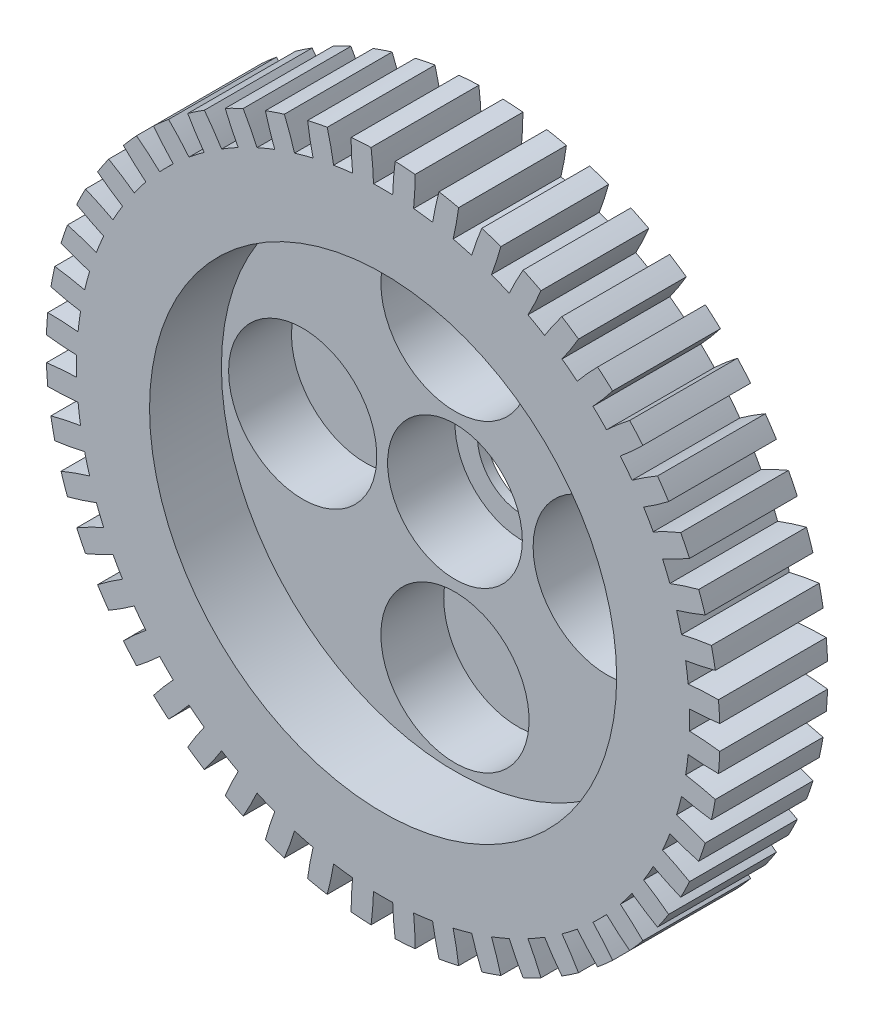
SolidWorks part; units mm, degrees
ref_plane "Piano frontale" through (0, 0, 0) normal (0, 0, 1) x (1, 0, 0)
ref_plane "Piano superiore" through (0, 0, 0) normal (0, 1, 0) x (1, 0, 0)
ref_plane "Piano destro" through (0, 0, 0) normal (1, 0, 0) x (0, 0, -1)
sketch "Schizzo1" plane through (0, 0, 0) normal (0, 0, 1) x (1, 0, 0)
  circle A0 centre (0, 0) radius 37.5
  dimension "D1" = 75
extrude "Estrusione-Estrusione2" add sketch "Schizzo1" along normal blind 12
sketch "Schizzo8" plane through (0, 0, 0) normal (0, 0, -1) x (-1, 0, 0)
  circle A0 centre (0, 0) radius 30
  dimension "D1" = 60
extrude "Taglio-Estrusione4" cut sketch "Schizzo8" against normal blind 2
sketch "Schizzo2" plane through (0, 0, 12) normal (0, 0, 1) x (1, 0, 0)
  circle A0 centre (0, 0) radius 26
  dimension "D1" = 52
extrude "Taglio-Estrusione1" cut sketch "Schizzo2" against normal blind 8
sketch "Schizzo4" plane through (0, 0, 0) normal (0, 0, -1) x (-1, 0, 0)
  circle A0 centre (0, 0) radius 8.5
  circle A1 centre (0, 0) radius 5
  dimension "D1" = 17
  dimension "D2" = 10
extrude "Estrusione-Estrusione3" add sketch "Schizzo4" along normal blind 6.5 from surface at -2 starting at face at (-30, 0, 2)
sketch "Schizzo3" plane through (0, 0, 4) normal (0, 0, 1) x (1, 0, 0)
  circle A0 centre (0, 0) radius 7.5
  dimension "D1" = 15
extrude "Taglio-Estrusione2" cut sketch "Schizzo3" against normal blind 7.5
sketch "Schizzo5" plane through (0, 0, 0) normal (0, 0, -1) x (-1, 0, 0)
  line L1 (-26.2, 0) -> (26.2, 0) construction
  circle A2 centre (0, 16.95) radius 9.25
  circle A7 centre (16.95, 0) radius 9.25
  circle A9 centre (0, -16.95) radius 9.25
  circle A10 centre (-16.95, 0) radius 9.25
  point P18 (0, 0)
  dimension "D1" = 18.5
  dimension "D2" = 4
  dimension "D4" = 52.4
extrude "Estrusione-Estrusione6" add sketch "Schizzo5" along normal blind 6.5 from surface at -2 starting at face at (-8.5, 0, 2)
sketch "Schizzo6" plane through (0, 0, -4.5) normal (0, 0, -1) x (-1, 0, 0)
  line L0 (0, 0) -> (0, 16.95) construction
  circle A0 centre (0, 16.95) radius 8.25
  circle A4 centre (16.95, 0) radius 8.25
  circle A5 centre (0, -16.95) radius 8.25
  circle A6 centre (-16.95, 0) radius 8.25
  dimension "D1" = 16.5
  dimension "D3" = 16.95
  dimension "D2" = 4
extrude "Taglio-Estrusione3" cut sketch "Schizzo6" along normal blind 7 from offset 8.5 offset against normal yes
sketch "Schizzo10" plane through (0, 0, 12) normal (0, 0, 1) x (1, 0, 0)
  line L0 (0, 0) -> (37.5, 0) construction
  line L1 (0, 0) -> (34.1083, -1.0677) construction
  line L2 (0, 0) -> (34.1083, 1.0677) construction
  arc A0 (35.9807, -1.178) -> (35.9807, 1.178) centre (0, 0) ccw construction
  arc A2 (34.1083, -1.0677) -> (34.1083, 1.0677) centre (0, 0) ccw
  arc A3 (37.4761, -1.3399) -> (37.4761, 1.3399) centre (0, 0) ccw
  circle A4 centre (0, 0) radius 37.5 construction
  spline S0 degree 4 poles (24.9625, -68.4576) (25.0835, -68.4874) (25.3257, -68.5458) (25.8112, -68.6578) (26.5426, -68.8117) (27.2776, -68.9478) (28.0156, -69.066) (28.7518, -69.1692) (29.3644, -69.243) (29.9762, -69.3049) (30.5873, -69.3549) (31.0764, -69.3879) (31.5666, -69.4138) (32.0556, -69.4328) (32.5818, -69.4453) (33.1334, -69.4505) (33.7369, -69.4447) (34.2613, -69.4315) (34.7521, -69.4104) (35.213, -69.3851) (35.466, -69.3686) (35.981, -69.3305) (36.3975, -69.2924) (36.846, -69.2464) (37.2899, -69.1949) (37.7329, -69.1376) (38.1752, -69.0744) (38.6168, -69.0055) (39.0573, -68.9309) (39.8265, -68.7901) (42.0132, -68.3305) (44.9107, -67.4661) (48.0036, -66.1458) (51.3092, -64.2674) (53.8863, -62.4893) (56.3007, -60.4921) (58.8065, -57.9338) (61.0314, -55.1278) (62.7111, -52.4827) (63.9471, -50.1005) (65.0135, -47.6395) (65.9064, -45.1086) (66.8884, -41.2947) (67.5021, -36.038) (67.1632, -29.8392) (65.5656, -23.8379) (63.2992, -18.9535) (60.6273, -14.8177) (58.0435, -11.7211) (55.4291, -9.2684) (52.935, -7.3757) (51.0649, -6.1515) (49.5199, -5.2516) (48.1287, -4.5357) (46.911, -3.9746) (45.8806, -3.5426) (45.0478, -3.2186) (44.2065, -2.9165) (43.3582, -2.6364) (42.5055, -2.3796) (41.6523, -2.1461) (40.7935, -1.9355) (39.9396, -1.7479) (39.0706, -1.582) (38.2159, -1.4388) (37.3264, -1.3169) (36.489, -1.219) (35.6426, -1.1482) (35.039, -1.1055) (34.3288, -1.0747) (34.0395, -1.0648) (33.5646, -1.0543) (33.0275, -1.0483) (32.492, -1.0532) (31.8232, -1.0694) (31.1807, -1.0987) (30.5266, -1.14) (29.8794, -1.1939) (29.2303, -1.2599) (28.5841, -1.3383) (27.9388, -1.4289) (27.2957, -1.5318) (26.4941, -1.6756) (25.6965, -1.8397) (24.9033, -2.0238) (24.2727, -2.1872) (23.9584, -2.2728) (23.8016, -2.3166) knots 0 0 0 0 0 0.003984 0.007969 0.015937 0.023906 0.02789 0.031875 0.039718 0.04364 0.047561 0.051483 0.055404 0.059326 0.063248 0.068241 0.073234 0.078227 0.080724 0.08322 0.086793 0.090366 0.09394 0.097513 0.101086 0.104659 0.108232 0.111805 0.115378 0.118951 0.133243 0.183267 0.211851 0.226144 0.254728 0.283313 0.311898 0.340482 0.369067 0.383359 0.397652 0.426236 0.454821 0.509105 0.566275 0.623444 0.652029 0.680613 0.72349 0.752075 0.766367 0.78066 0.794952 0.809244 0.81639 0.823537 0.830683 0.837829 0.844975 0.852121 0.859142 0.866163 0.873184 0.880205 0.887226 0.894247 0.901268 0.908289 0.912473 0.916656 0.919261 0.921865 0.927074 0.932283 0.937492 0.942701 0.94791 0.953119 0.958328 0.963537 0.968746 0.973955 0.979164 0.989582 0.994791 1 1 1 1 1 construction
  spline S1 degree 4 poles (37.4761, -1.3399) (37.3325, -1.3211) (36.9741, -1.276) (36.4092, -1.2123) (35.6426, -1.1482) (35.039, -1.1055) (34.4316, -1.0792) (34.2172, -1.0711) (34.1083, -1.0677) knots 0.889607 0.889607 0.889607 0.889607 0.889607 0.894247 0.901268 0.908289 0.912473 0.916656 0.916656 0.916656 0.916656 0.916656
  spline S2 degree 4 poles (24.9625, 68.4576) (25.0835, 68.4874) (25.3257, 68.5458) (25.8112, 68.6578) (26.5426, 68.8117) (27.2776, 68.9478) (28.0156, 69.066) (28.7518, 69.1692) (29.3644, 69.243) (29.9762, 69.3049) (30.5873, 69.3549) (31.0764, 69.3879) (31.5666, 69.4138) (32.0556, 69.4328) (32.5818, 69.4453) (33.1334, 69.4505) (33.7369, 69.4447) (34.2613, 69.4315) (34.7521, 69.4104) (35.213, 69.3851) (35.466, 69.3686) (35.981, 69.3305) (36.3975, 69.2924) (36.846, 69.2464) (37.2899, 69.1949) (37.7329, 69.1376) (38.1752, 69.0744) (38.6168, 69.0055) (39.0573, 68.9309) (39.8265, 68.7901) (42.0132, 68.3305) (44.9107, 67.4661) (48.0036, 66.1458) (51.3092, 64.2674) (53.8863, 62.4893) (56.3007, 60.4921) (58.8065, 57.9338) (61.0314, 55.1278) (62.7111, 52.4827) (63.9471, 50.1005) (65.0135, 47.6395) (65.9064, 45.1086) (66.8884, 41.2947) (67.5021, 36.038) (67.1632, 29.8392) (65.5656, 23.8379) (63.2992, 18.9535) (60.6273, 14.8177) (58.0435, 11.7211) (55.4291, 9.2684) (52.935, 7.3757) (51.0649, 6.1515) (49.5199, 5.2516) (48.1287, 4.5357) (46.911, 3.9746) (45.8806, 3.5426) (45.0478, 3.2186) (44.2065, 2.9165) (43.3582, 2.6364) (42.5055, 2.3796) (41.6523, 2.1461) (40.7935, 1.9355) (39.9396, 1.7479) (39.0706, 1.582) (38.2159, 1.4388) (37.3264, 1.3169) (36.489, 1.219) (35.6426, 1.1482) (35.039, 1.1055) (34.3288, 1.0747) (34.0395, 1.0648) (33.5646, 1.0543) (33.0275, 1.0483) (32.492, 1.0532) (31.8232, 1.0694) (31.1807, 1.0987) (30.5266, 1.14) (29.8794, 1.1939) (29.2303, 1.2599) (28.5841, 1.3383) (27.9388, 1.4289) (27.2957, 1.5318) (26.4941, 1.6756) (25.6965, 1.8397) (24.9033, 2.0238) (24.2727, 2.1872) (23.9584, 2.2728) (23.8016, 2.3166) knots 0 0 0 0 0 0.003984 0.007969 0.015937 0.023906 0.02789 0.031875 0.039718 0.04364 0.047561 0.051483 0.055404 0.059326 0.063248 0.068241 0.073234 0.078227 0.080724 0.08322 0.086793 0.090366 0.09394 0.097513 0.101086 0.104659 0.108232 0.111805 0.115378 0.118951 0.133243 0.183267 0.211851 0.226144 0.254728 0.283313 0.311898 0.340482 0.369067 0.383359 0.397652 0.426236 0.454821 0.509105 0.566275 0.623444 0.652029 0.680613 0.72349 0.752075 0.766367 0.78066 0.794952 0.809244 0.81639 0.823537 0.830683 0.837829 0.844975 0.852121 0.859142 0.866163 0.873184 0.880205 0.887226 0.894247 0.901268 0.908289 0.912473 0.916656 0.919261 0.921865 0.927074 0.932283 0.937492 0.942701 0.94791 0.953119 0.958328 0.963537 0.968746 0.973955 0.979164 0.989582 0.994791 1 1 1 1 1 construction
  spline S3 degree 4 poles (37.4761, 1.3399) (37.3325, 1.3211) (36.9741, 1.276) (36.4092, 1.2123) (35.6426, 1.1482) (35.039, 1.1055) (34.4316, 1.0792) (34.2172, 1.0711) (34.1083, 1.0677) knots 0.889607 0.889607 0.889607 0.889607 0.889607 0.894247 0.901268 0.908289 0.912473 0.916656 0.916656 0.916656 0.916656 0.916656
  point P5 (37.5, 0)
  dimension "D1" = 72
  dimension "D2" = 68.25
  dimension "D3" = 2.356
extrude "Taglio-Estrusione6" cut sketch "Schizzo10" against normal through all
pattern_circular "RipetizioneCircolare2" count 48 over 360 about axis through (0, 0, 0) along (0, 0, -1) of "Taglio-Estrusione6"
